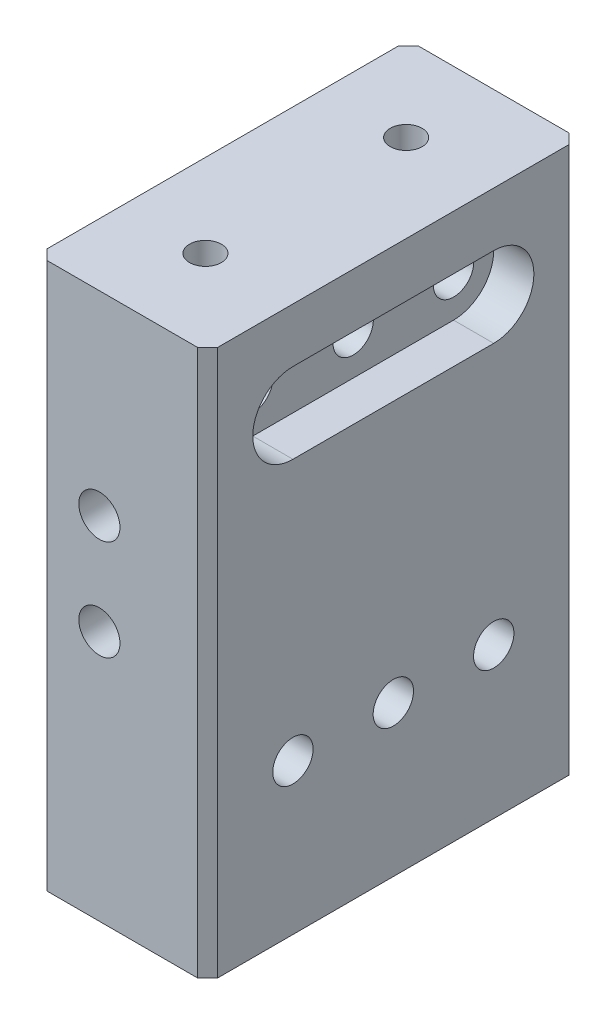
SolidWorks part; units mm, degrees
material "PET"
ref_plane "Front Plane" through (0, 0, 0) normal (0, 0, 1) x (1, 0, 0)
ref_plane "Top Plane" through (0, 0, 0) normal (0, 1, 0) x (1, 0, 0)
ref_plane "Right Plane" through (0, 0, 0) normal (1, 0, 0) x (0, 0, -1)
sketch "Sketch1" plane through (0, 0, 0) normal (0, 1, 0) x (1, 0, 0)
  line L1 (-10.795, -23.495) -> (10.795, -23.495)
  line L2 (-10.795, -23.495) -> (-10.795, 23.495)
  line L3 (-10.795, 23.495) -> (10.795, 23.495)
  line L4 (10.795, -23.495) -> (10.795, 23.495)
  line L5 (-10.795, -23.495) -> (10.795, 23.495) construction
  line L6 (-10.795, 23.495) -> (10.795, -23.495) construction
  point P0 (0, 0)
  dimension "D1" = 21.59
  dimension "D2" = 46.99
extrude "Boss-Extrude1" add sketch "Sketch1" along normal mid plane 63.5
sketch "Sketch2" plane through (0, 0, 23.495) normal (0, 0, 1) x (1, 0, 0)
  line L5 (-10.795, 31.75) -> (10.795, 31.75) construction
  circle A1 centre (-2.8956, 0) radius 2.6035
  circle A2 centre (-2.8956, 12.7) radius 2.6035
  circle A3 centre (-2.8956, -12.7) radius 2.6035
  dimension "D3" = 19.05
  dimension "D1" = 13.6906
  dimension "D2" = 5.207
  dimension "D4" = 12.7
  dimension "D5" = 12.7
extrude "Cut-Extrude1" cut sketch "Sketch2" against normal through all contours A2 | A1
sketch "Sketch4" plane through (10.795, 0, 0) normal (1, 0, 0) x (0, 0, -1)
  line L0 (-23.495, 31.75) -> (23.495, 31.75) construction
  circle A0 centre (-12.7, 25.4) radius 2.5527
  circle A1 centre (12.7, 25.4) radius 2.5527
  circle A2 centre (0, 25.4) radius 2.5527
  dimension "D5" = 5.1054
  dimension "D1" = 6.35
  dimension "D3" = 12.7
  dimension "D4" = 12.7
extrude "Cut-Extrude3" cut sketch "Sketch4" against normal through all
sketch "Sketch7" plane through (10.795, 0, 0) normal (1, 0, 0) x (0, 0, -1)
  line L0 (-12.7, 25.4) -> (12.7, 25.4) construction
  line L1 (-12.7, 30.48) -> (12.7, 30.48)
  line L2 (-12.7, 20.32) -> (12.7, 20.32)
  arc A0 (-12.7, 30.48) -> (-12.7, 20.32) centre (-12.7, 25.4) ccw
  arc A1 (12.7, 20.32) -> (12.7, 30.48) centre (12.7, 25.4) ccw
  point P4 (0, 25.4)
  dimension "D1" = 5.08
extrude "Cut-Extrude5" cut sketch "Sketch7" against normal blind 5.08
sketch "Sketch8" plane through (0, 31.75, 0) normal (0, 1, 0) x (1, 0, 0)
  line L4 (-10.795, -23.495) -> (10.795, -23.495)
  line L5 (10.795, -23.495) -> (10.795, 23.495)
  line L6 (10.795, 23.495) -> (-10.795, 23.495)
  line L7 (-10.795, 23.495) -> (-10.795, -23.495)
  line L8 (-10.795, -23.495) -> (10.795, -23.495)
  line L9 (10.795, -23.495) -> (10.795, 23.495)
  line L10 (10.795, 23.495) -> (-10.795, 23.495)
  line L11 (-10.795, 23.495) -> (-10.795, -23.495)
  dimension "D1" = 0
extrude "Boss-Extrude2" add sketch "Sketch8" along normal blind 5.588
sketch "Sketch9" plane through (0, 37.338, 0) normal (0, 1, 0) x (1, 0, 0)
  line L0 (-10.795, 0) -> (10.795, 0) construction
  line L1 (-10.795, 23.495) -> (-10.795, -23.495) construction
  line L2 (10.795, -23.495) -> (10.795, 23.495) construction
  circle A0 centre (-0.2794, 12.6969) radius 2.0193
  circle A2 centre (-0.2794, -12.6969) radius 2.0193
  dimension "D2" = 4.0386
  dimension "D1" = 12.7
  dimension "D3" = 10.5156
extrude "Cut-Extrude6" cut sketch "Sketch9" against normal blind 5.08
sketch "Sketch10" plane through (10.795, 0, 0) normal (1, 0, 0) x (0, 0, -1)
  line L1 (-23.495, -31.75) -> (23.495, -31.75) construction
  circle A0 centre (0, -12.7) radius 2.5527
  circle A1 centre (12.7, -12.7) radius 2.5527
  circle A2 centre (-12.7, -12.7) radius 2.5527
  dimension "D1" = 5.1054
  dimension "D2" = 12.7
  dimension "D3" = 12.7
  dimension "D4" = 19.05
extrude "Cut-Extrude7" cut sketch "Sketch10" against normal through all
chamfer "Chamfer1" distance 1.27 angle 45 4 edges at (-10.795, 2.794, 23.495) (10.795, 2.794, 23.495) (-10.795, 2.794, -23.495) (10.795, 2.794, -23.495)
